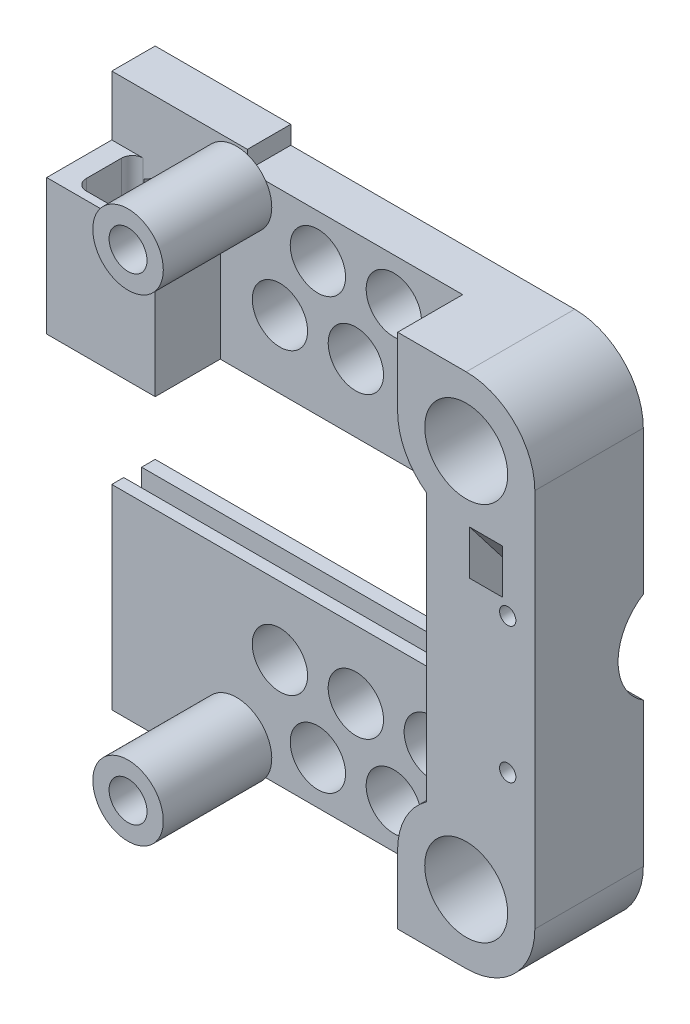
SolidWorks part; units mm, degrees
material "ABS"
ref_plane "Plano frontal" through (0, 0, 0) normal (0, 0, 1) x (1, 0, 0)
ref_plane "Plano superior" through (0, 0, 0) normal (0, 1, 0) x (1, 0, 0)
ref_plane "Plano direito" through (0, 0, 0) normal (1, 0, 0) x (0, 0, -1)
sketch "Esboço1" plane through (0, 0, 0) normal (0, 0, 1) x (1, 0, 0)
  line L0 (0, 0) -> (47.1208, 0) construction
  line L1 (12.65, 35) -> (12.65, -35)
  line L2 (0, 47.65) -> (-72.35, 47.65)
  line L3 (-72.35, 47.65) -> (-72.35, -47.65)
  line L4 (0, -47.65) -> (-72.35, -47.65)
  circle A0 centre (0, 35) radius 7.65
  arc A1 (12.65, -35) -> (0, -47.65) centre (0, -35) cw
  arc A2 (12.65, 35) -> (0, 47.65) centre (0, 35) ccw
  circle A3 centre (0, -35) radius 7.65
  point P10 (12.65, 0)
  point P15 (-72.35, 0)
  dimension "D2" = 15.3
  dimension "D3" = 5
  dimension "D1" = 70
  dimension "D4" = 85
extrude "Ressalto-extrusão1" add sketch "Esboço1" along normal blind 20
sketch "Esboço2" plane through (0, 0, 0) normal (0, 1, 0) x (1, 0, 0)
  line L0 (-52.35, -20) -> (-52.35, 0)
  line L2 (-32.5, 20) -> (-62.35, 20) construction
  line L3 (-62.35, 20) -> (-62.35, 0) construction
  line L4 (-52.35, 0) -> (-77.35, 0)
  line L5 (-77.35, 0) -> (-77.35, -20)
  line L6 (-72.35, -20) -> (0, -20) construction
  line L7 (-77.35, -20) -> (-52.35, -20)
  line L8 (-72.35, -20) -> (-72.35, 0) construction
  line L9 (-72.35, 0) -> (0, 0) construction
  dimension "D1" = 5
  dimension "D2" = 15
  dimension "D3" = 10
  dimension "D4" = 20
  dimension "D5" = 0
extrude "Ressalto-extrusão2" add sketch "Esboço2" along normal mid plane 102
sketch "Esboço3" plane through (-77.35, 0, 0) normal (-1, 0, 0) x (0, 0, 1)
  line L0 (13.8, 15) -> (5.8, 15)
  line L1 (20, 51) -> (20, -51) construction
  line L2 (5.8, 15) -> (5.8, 20)
  line L3 (5.8, 20) -> (2.5, 20)
  line L4 (2.5, 20) -> (2.5, 15)
  line L5 (2.5, 15) -> (-3, 15)
  line L7 (-3, 15) -> (-3, -15)
  line L8 (13.8, 15) -> (13.8, -15)
  line L9 (0, 0) -> (20, 0) construction
  line L10 (2.5, -15) -> (-3, -15)
  line L11 (2.5, -20) -> (2.5, -15)
  line L12 (5.8, -20) -> (2.5, -20)
  line L13 (5.8, -15) -> (5.8, -20)
  line L14 (13.8, -15) -> (5.8, -15)
  line L15 (0, -35) -> (0, 35) construction
  line L16 (0, 51) -> (0, -51) construction
  dimension "D1" = 3.3
  dimension "D2" = 30
  dimension "D3" = 5
  dimension "D4" = 8
  dimension "D5" = 3
  dimension "D6" = 2.5
extrude "Corte-extrusão1" cut sketch "Esboço3" against normal offset from surface (78 mm away) 12 up to face at (12.65, 0, 10)
sketch "Esboço4" plane through (0, 0, 20) normal (0, 0, 1) x (1, 0, 0)
  line L1 (-77.35, 51) -> (-77.35, -51) construction
  line L2 (-57.35, 40) -> (-77.35, 40)
  line L3 (-57.35, 40) -> (-57.35, 15)
  line L4 (-57.35, 15) -> (-77.35, 15)
  line L5 (12.65, -35) -> (12.65, 35) construction
  line L6 (-77.35, 40) -> (-77.35, 15)
  line L10 (-77.35, 51) -> (-77.35, -51)
  line L11 (-12.65, -35) -> (-12.65, -47.65)
  line L12 (-12.65, 35) -> (-12.65, 47.65)
  line L13 (-77.35, 51) -> (-77.35, -51)
  line L14 (-77.35, -51) -> (-52.35, -51)
  line L15 (0, 0) -> (9.243, 0) construction
  line L16 (-7.35, -0.3234) -> (-7.35, 24.7044)
  line L17 (-77.35, -51) -> (-52.35, -51)
  line L22 (-52.35, -51) -> (-52.35, -47.65)
  line L23 (-52.35, -51) -> (-52.35, -47.65)
  line L24 (-52.35, -47.65) -> (0, -47.65)
  line L25 (-52.35, -47.65) -> (0, -47.65)
  line L26 (-52.35, 47.65) -> (-52.35, 51)
  line L27 (12.65, -35) -> (12.65, 35)
  line L28 (0, 47.65) -> (-52.35, 47.65)
  line L29 (-52.35, 47.65) -> (-52.35, 51)
  line L30 (-52.35, 51) -> (-77.35, 51)
  line L31 (-52.35, 51) -> (-77.35, 51)
  line L39 (-7.35, -24.7044) -> (-7.35, -0.3234)
  line L40 (-12.65, 47.65) -> (-52.35, 47.65)
  arc A0 (-12.65, 35) -> (-7.35, 24.7044) centre (0, 35) ccw
  arc A1 (-7.35, -24.7044) -> (-12.65, -35) centre (0, -35) ccw
  arc A2 (0, -47.65) -> (12.65, -35) centre (0, -35) ccw
  arc A3 (12.65, 35) -> (0, 47.65) centre (0, 35) ccw
  circle A4 centre (0, 35) radius 7.65 construction
  dimension "D6" = 5
  dimension "D1" = 20
  dimension "D2" = 25
  dimension "D3" = 20
  dimension "D5" = 0
extrude "Corte-extrusão4" cut sketch "Esboço4" against normal blind 12
sketch "Esboço6" plane through (0, 0, 8) normal (0, 0, 1) x (1, 0, 0)
  line L0 (0, 0) -> (33.6798, 0) construction
  line L2 (12.65, -35) -> (12.65, 35) construction
  circle A0 centre (7.65, 12.5) radius 1.5
  circle A1 centre (7.65, -12.5) radius 1.5
  dimension "D2" = 3
  dimension "D1" = 25
  dimension "D3" = 5
extrude "Corte-extrusão6" cut sketch "Esboço6" against normal through all both and the other way through all
sketch "Esboço7" plane through (12.65, 0, 0) normal (1, 0, 0) x (0, 0, -1)
  line L0 (0, -35) -> (0, 35) construction
  circle A0 centre (5.3491, 0) radius 10
  point P6 (0, 0)
  dimension "D1" = 20
extrude "Corte-extrusão7" cut sketch "Esboço7" against normal blind 8
sketch "Esboço9" plane through (0, 40, 0) normal (0, 1, 0) x (1, 0, 0)
  line L1 (-73.55, -8) -> (-61.15, -8)
  line L2 (-73.55, -8) -> (-73.55, -18.5)
  line L3 (-73.55, -18.5) -> (-61.15, -18.5)
  line L4 (-61.15, -8) -> (-61.15, -18.5)
  line L5 (-73.55, -8) -> (-61.15, -18.5) construction
  line L6 (-73.55, -18.5) -> (-61.15, -8) construction
  line L8 (-57.35, -20) -> (-77.35, -20) construction
  line L9 (-52.35, -8) -> (-77.35, -8) construction
  point P0 (-67.35, -13.25)
  point P14 (-67.35, -20)
  dimension "D1" = 12.4
  dimension "D2" = 10.5
extrude "Corte-extrusão8" cut sketch "Esboço9" against normal up to surface (25 mm away) up to face at (-35.35, 15, 11.9)
sketch "Esboço10" plane through (0, 40, 0) normal (0, 1, 0) x (1, 0, 0)
  line L1 (-77.35, -8) -> (-57.35, -8)
  line L2 (-77.35, -8) -> (-77.35, -20)
  line L3 (-77.35, -20) -> (-57.35, -20)
  line L4 (-57.35, -8) -> (-57.35, -20)
  line L5 (-71.55, -8) -> (-63.15, -8)
  line L6 (-73.55, -10) -> (-73.55, -16.5)
  line L7 (-71.55, -18.5) -> (-63.15, -18.5)
  line L8 (-61.15, -10) -> (-61.15, -16.5)
  line L9 (-73.55, -8) -> (-61.15, -18.5) construction
  line L10 (-73.55, -18.5) -> (-61.15, -8) construction
  arc A0 (-73.55, -16.5) -> (-71.55, -18.5) centre (-71.55, -16.5) ccw
  arc A1 (-63.15, -18.5) -> (-61.15, -16.5) centre (-63.15, -16.5) ccw
  arc A2 (-63.15, -8) -> (-61.15, -10) centre (-63.15, -10) cw
  arc A3 (-71.55, -8) -> (-73.55, -10) centre (-71.55, -10) ccw
  point P6 (-67.35, -13.25)
  line M1 (-61.15, -8) -> (-61.15, -18.5)
  line M2 (-61.15, -18.5) -> (-73.55, -18.5)
  line M3 (-73.55, -18.5) -> (-73.55, -8)
  line M4 (-73.55, -8) -> (-77.35, -8)
  line M5 (-77.35, -8) -> (-77.35, -20)
  line M6 (-77.35, -20) -> (-57.35, -20)
  line M7 (-57.35, -20) -> (-57.35, -8)
  line M8 (-57.35, -8) -> (-61.15, -8)
  dimension "D1" = 2
extrude "Ressalto-extrusão3" add sketch "Esboço10" against normal offset from surface (15.5 mm away) 9.5 contours M8 M1 M2 M3 M4 M5 M6 M7 | A3 L1 M3 | A0 M3 M2 | A1 M2 M1 | L1 A2 M1 up to face at (-67.35, 15, 13.25)
sketch "Esboço11" [suppressed] plane through (0, 0, 0) normal (0, 1, 0) x (1, 0, 0)
  line L0 (-29.15, -11) -> (-16.15, -11) construction
  line L1 (-32.65, -8) -> (-12.65, -8)
  line L2 (-29.15, -14.5) -> (-16.15, -14.5)
  line L3 (-29.15, -11) -> (-16.15, -11) construction
  line L4 (-29.15, -9.5) -> (-16.15, -9.5)
  line L5 (-29.15, -12.5) -> (-16.15, -12.5)
  line L6 (-57.35, -8) -> (-12.65, -8) construction
  line L7 (-12.65, -8) -> (-12.65, -20) construction
  line L8 (-32.65, -11) -> (-32.65, -8)
  line L9 (-12.65, -11) -> (-12.65, -8)
  arc A0 (-32.65, -11) -> (-29.15, -14.5) centre (-29.15, -11) ccw
  arc A1 (-16.15, -14.5) -> (-12.65, -11) centre (-16.15, -11) ccw
  arc A2 (-29.15, -9.5) -> (-29.15, -12.5) centre (-29.15, -11) ccw
  arc A3 (-16.15, -12.5) -> (-16.15, -9.5) centre (-16.15, -11) ccw
  point P2 (-22.5, -11)
  point P7 (-22.65, -11)
  dimension "D1" = 13
  dimension "D3" = 3.5
  dimension "D5" = 1.5
  dimension "D2" = 3
  dimension "D4" = 3.5
sketch "Esboço12" plane through (0, 0, 8) normal (0, 0, 1) x (1, 0, 0)
  line L2 (0, 0) -> (-80.3757, 0) construction
  line L3 (-71.55, 35) -> (-63.15, 35) construction
  line L4 (-77.35, 51) -> (-77.35, 40) construction
  line L5 (-71.55, 24.5) -> (-71.55, 40) construction
  line L6 (-63.15, 24.5) -> (-63.15, 40) construction
  line L7 (-61.15, 40) -> (-63.15, 40) construction
  line L8 (-77.35, -15) -> (-77.35, -51) construction
  circle A2 centre (-54.35, -44) radius 1.65
  circle A3 centre (-54.35, 44) radius 1.65
  circle A4 centre (-68.55, 35) radius 1.65
  point P29 (-62.15, 40)
  dimension "D1" = 23
  dimension "D5" = 88
  dimension "D6" = 23
  dimension "D7" = 5
  dimension "D8" = 3
extrude "Corte-extrusão9" cut sketch "Esboço12" against normal blind 10
sketch "Esboço14" plane through (0, 0, 8) normal (0, 0, 1) x (1, 0, 0)
  line L1 (-71.45, 36.6743) -> (-71.45, 33.3257)
  line L2 (-71.45, 33.3257) -> (-68.55, 31.6514)
  line L3 (-68.55, 31.6514) -> (-65.65, 33.3257)
  line L4 (-65.65, 33.3257) -> (-65.65, 36.6743)
  line L5 (-65.65, 36.6743) -> (-68.55, 38.3486)
  line L6 (-68.55, 38.3486) -> (-71.45, 36.6743)
  circle A0 centre (-68.55, 35) radius 2.9 construction
  dimension "D1" = 5.8
extrude "Corte-extrusão11" cut sketch "Esboço14" against normal blind 2
sketch "Esboço15" plane through (-77.35, 0, 0) normal (-1, 0, 0) x (0, 0, 1)
  line L0 (2.5, 20) -> (1.2, 20)
  line L1 (8, -24.7044) -> (8, -15) construction
  line L2 (1.2, 20) -> (1.2, -25)
  line L4 (1.2, -25) -> (8, -40)
  line L6 (8, -40) -> (8, -15)
  line L7 (8, -15) -> (2.5, -15)
  line L8 (2.5, -15) -> (2.5, 20)
  line L9 (0, 51) -> (0, 15) construction
  dimension "D1" = 10
  dimension "D2" = 1.2
  dimension "D3" = 25
extrude "Corte-extrusão12" [suppressed] cut sketch "Esboço15" against normal blind 14
sketch "Esboço16" plane through (0, 0, 8) normal (0, 0, 1) x (1, 0, 0)
  line L0 (0, 0) -> (-86.7828, 0) construction
  circle A0 centre (-54.35, 44) radius 3.5
  circle A1 centre (-54.35, 44) radius 6.5
  circle A3 centre (-54.35, -44) radius 6.5
  circle A4 centre (-54.35, -44) radius 3.5
  dimension "D1" = 13
  dimension "D2" = 7
extrude "Ressalto-extrusão4" add sketch "Esboço16" along normal blind 20
sketch "Esboço17" plane through (0.65, 0, 0) normal (-1, 0, 0) x (0, 0, 1)
  line L2 (11.8, 4.3767) -> (11.8, -3.75)
  line L3 (11.8, -3.75) -> (5, -3.75)
  line L4 (5, 3.75) -> (5, -3.75)
  line L5 (11.8, 3.75) -> (5, -3.75) construction
  line L6 (11.8, -3.75) -> (5, 3.75) construction
  line L7 (11.8, 4.3767) -> (20, 15)
  line L8 (20, 15) -> (20, 23.1829)
  line L9 (20, 40) -> (20, 15) construction
  line L10 (20, 23.1829) -> (5, 3.75)
  line L11 (0, 15) -> (0, -15) construction
  point P0 (8.4, 0)
  dimension "D1" = 6.8
  dimension "D2" = 5
  dimension "D3" = 5
  dimension "D4" = 7.5
extrude "Corte-extrusão13" cut sketch "Esboço17" against normal blind 6
sketch "Esboço18" plane through (0, 0, 8) normal (0, 0, 1) x (1, 0, 0)
  line L0 (-46.35, -27.5256) -> (-32.35, -27.5256) construction
  line L1 (-32.35, -27.5256) -> (-39.35, -39.65) construction
  line L2 (-39.35, -39.65) -> (-46.35, -27.5256) construction
  line L3 (-48.9716, -47.65) -> (-12.65, -47.65) construction
  line L4 (12.65, -35) -> (12.65, 35) construction
  line L5 (0, 0) -> (-72.0173, 0) construction
  line L6 (-32.35, -27.5256) -> (-25.35, -39.65) construction
  line L7 (-25.35, -39.65) -> (-39.35, -39.65) construction
  line L8 (-32.35, -27.5256) -> (-18.35, -27.5256) construction
  line L9 (-18.35, -27.5256) -> (-25.35, -39.65) construction
  line L10 (-18.35, 27.5256) -> (-25.35, 39.65) construction
  line L11 (-32.35, 27.5256) -> (-18.35, 27.5256) construction
  line L12 (-25.35, 39.65) -> (-39.35, 39.65) construction
  line L13 (-32.35, 27.5256) -> (-25.35, 39.65) construction
  line L14 (-39.35, 39.65) -> (-46.35, 27.5256) construction
  line L15 (-32.35, 27.5256) -> (-39.35, 39.65) construction
  line L16 (-46.35, 27.5256) -> (-32.35, 27.5256) construction
  circle A0 centre (-39.35, -39.65) radius 5.1
  circle A1 centre (-32.35, -27.5256) radius 5.1
  circle A2 centre (-46.35, -27.5256) radius 5.1
  circle A3 centre (-25.35, -39.65) radius 5.1
  circle A4 centre (-18.35, -27.5256) radius 5.1
  circle A5 centre (-18.35, 27.5256) radius 5.1
  circle A6 centre (-25.35, 39.65) radius 5.1
  circle A7 centre (-46.35, 27.5256) radius 5.1
  circle A8 centre (-32.35, 27.5256) radius 5.1
  circle A9 centre (-39.35, 39.65) radius 5.1
  dimension "D1" = 10.2
  dimension "D2" = 14
  dimension "D3" = 8
  dimension "D4" = 45
extrude "Corte-extrusão14" cut sketch "Esboço18" against normal blind 10
